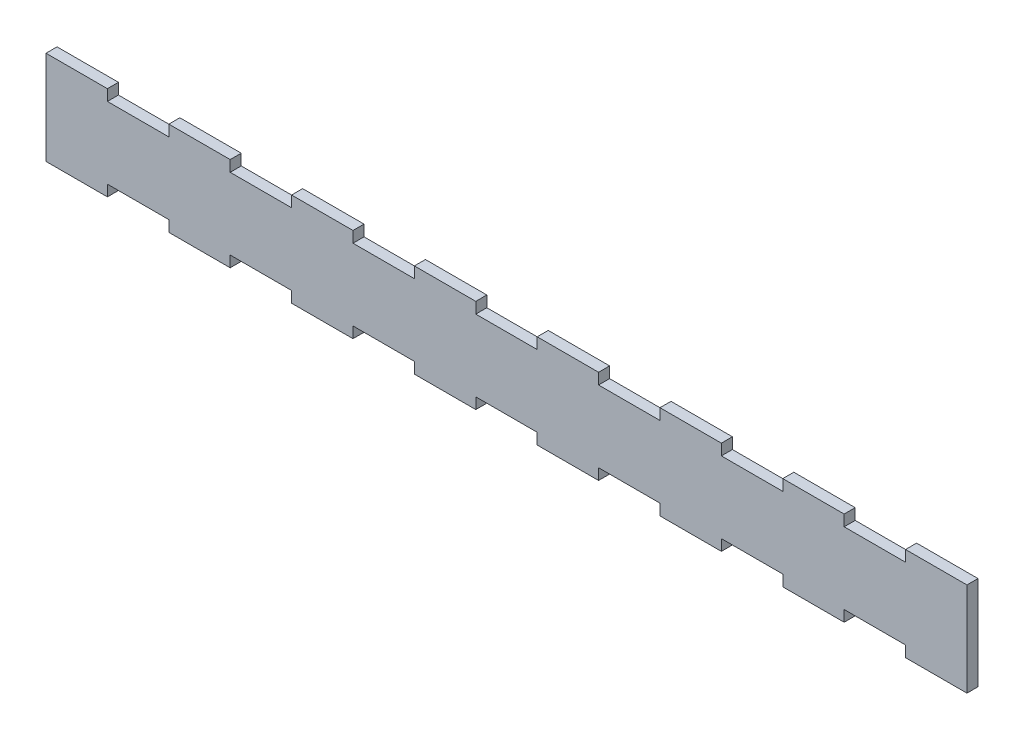
SolidWorks part; units mm, degrees
ref_plane "Front Plane" through (0, 0, 0) normal (0, 0, 1) x (1, 0, 0)
ref_plane "Top Plane" through (0, 0, 0) normal (0, 1, 0) x (1, 0, 0)
ref_plane "Right Plane" through (0, 0, 0) normal (1, 0, 0) x (0, 0, -1)
sketch "Sketch2" plane through (0, 0, 0) normal (0, 0, 1) x (1, 0, 0)
  line L35 (220.6639, 16.7457) -> (220.6639, 22.1457)
  line L88 (190.6639, 16.7457) -> (220.6639, 16.7457)
  line L89 (160.6639, 16.7457) -> (160.6639, -18.2543)
  line L109 (190.6639, -18.2543) -> (220.6639, -18.2543)
  line L111 (610.6639, 16.7457) -> (610.6639, -18.2543)
  line L113 (160.6639, 16.7457) -> (160.6639, 22.1457)
  line L115 (160.6639, 22.1457) -> (190.6639, 22.1457)
  line L116 (190.6639, 16.7457) -> (190.6639, 22.1457)
  line L119 (250.6639, 16.7457) -> (250.6639, 22.1457)
  line L120 (220.6639, 22.1457) -> (250.6639, 22.1457)
  line L121 (280.6639, 16.7457) -> (280.6639, 22.1457)
  line L123 (310.6639, 16.7457) -> (310.6639, 22.1457)
  line L124 (280.6639, 22.1457) -> (310.6639, 22.1457)
  line L125 (340.6639, 16.7457) -> (340.6639, 22.1457)
  line L127 (370.6639, 16.7457) -> (370.6639, 22.1457)
  line L128 (340.6639, 22.1457) -> (370.6639, 22.1457)
  line L129 (400.6639, 16.7457) -> (400.6639, 22.1457)
  line L131 (430.6639, 16.7457) -> (430.6639, 22.1457)
  line L132 (400.6639, 22.1457) -> (430.6639, 22.1457)
  line L133 (460.6639, 16.7457) -> (460.6639, 22.1457)
  line L135 (490.6639, 16.7457) -> (490.6639, 22.1457)
  line L136 (460.6639, 22.1457) -> (490.6639, 22.1457)
  line L137 (520.6639, 16.7457) -> (520.6639, 22.1457)
  line L139 (550.6639, 16.7457) -> (550.6639, 22.1457)
  line L140 (520.6639, 22.1457) -> (550.6639, 22.1457)
  line L141 (580.6639, 16.7457) -> (580.6639, 22.1457)
  line L143 (610.6639, 16.7457) -> (610.6639, 22.1457)
  line L144 (580.6639, 22.1457) -> (610.6639, 22.1457)
  line L145 (160.6639, -0.7543) -> (610.6639, -0.7543) construction
  line L147 (610.6639, -18.2543) -> (610.6639, -23.6543)
  line L148 (580.6639, -23.6543) -> (610.6639, -23.6543)
  line L149 (580.6639, -18.2543) -> (580.6639, -23.6543)
  line L151 (550.6639, -18.2543) -> (550.6639, -23.6543)
  line L152 (520.6639, -23.6543) -> (550.6639, -23.6543)
  line L153 (520.6639, -18.2543) -> (520.6639, -23.6543)
  line L155 (490.6639, -18.2543) -> (490.6639, -23.6543)
  line L156 (460.6639, -23.6543) -> (490.6639, -23.6543)
  line L157 (460.6639, -18.2543) -> (460.6639, -23.6543)
  line L159 (430.6639, -18.2543) -> (430.6639, -23.6543)
  line L160 (400.6639, -23.6543) -> (430.6639, -23.6543)
  line L161 (400.6639, -18.2543) -> (400.6639, -23.6543)
  line L163 (370.6639, -18.2543) -> (370.6639, -23.6543)
  line L164 (340.6639, -23.6543) -> (370.6639, -23.6543)
  line L165 (340.6639, -18.2543) -> (340.6639, -23.6543)
  line L167 (310.6639, -18.2543) -> (310.6639, -23.6543)
  line L168 (280.6639, -23.6543) -> (310.6639, -23.6543)
  line L169 (280.6639, -18.2543) -> (280.6639, -23.6543)
  line L171 (250.6639, -18.2543) -> (250.6639, -23.6543)
  line L172 (220.6639, -23.6543) -> (250.6639, -23.6543)
  line L173 (220.6639, -18.2543) -> (220.6639, -23.6543)
  line L174 (160.6639, -23.6543) -> (190.6639, -23.6543)
  line L175 (190.6639, -18.2543) -> (190.6639, -23.6543)
  line L177 (160.6639, -18.2543) -> (160.6639, -23.6543)
  line L178 (250.6639, 16.7457) -> (280.6639, 16.7457)
  line L179 (250.6639, -18.2543) -> (280.6639, -18.2543)
  line L180 (310.6639, -18.2543) -> (340.6639, -18.2543)
  line L181 (310.6639, 16.7457) -> (340.6639, 16.7457)
  line L182 (370.6639, 16.7457) -> (400.6639, 16.7457)
  line L183 (430.6639, 16.7457) -> (460.6639, 16.7457)
  line L184 (490.6639, 16.7457) -> (520.6639, 16.7457)
  line L185 (550.6639, 16.7457) -> (580.6639, 16.7457)
  line L186 (550.6639, -18.2543) -> (580.6639, -18.2543)
  line L187 (490.6639, -18.2543) -> (520.6639, -18.2543)
  line L188 (430.6639, -18.2543) -> (460.6639, -18.2543)
  line L189 (370.6639, -18.2543) -> (400.6639, -18.2543)
  dimension "D1" = 450
  dimension "D2" = 35
  dimension "D3" = 5.4
  dimension "D4" = 30
  dimension "D5" = 8
extrude "Boss-Extrude1" add sketch "Sketch2" along normal blind 5.4
